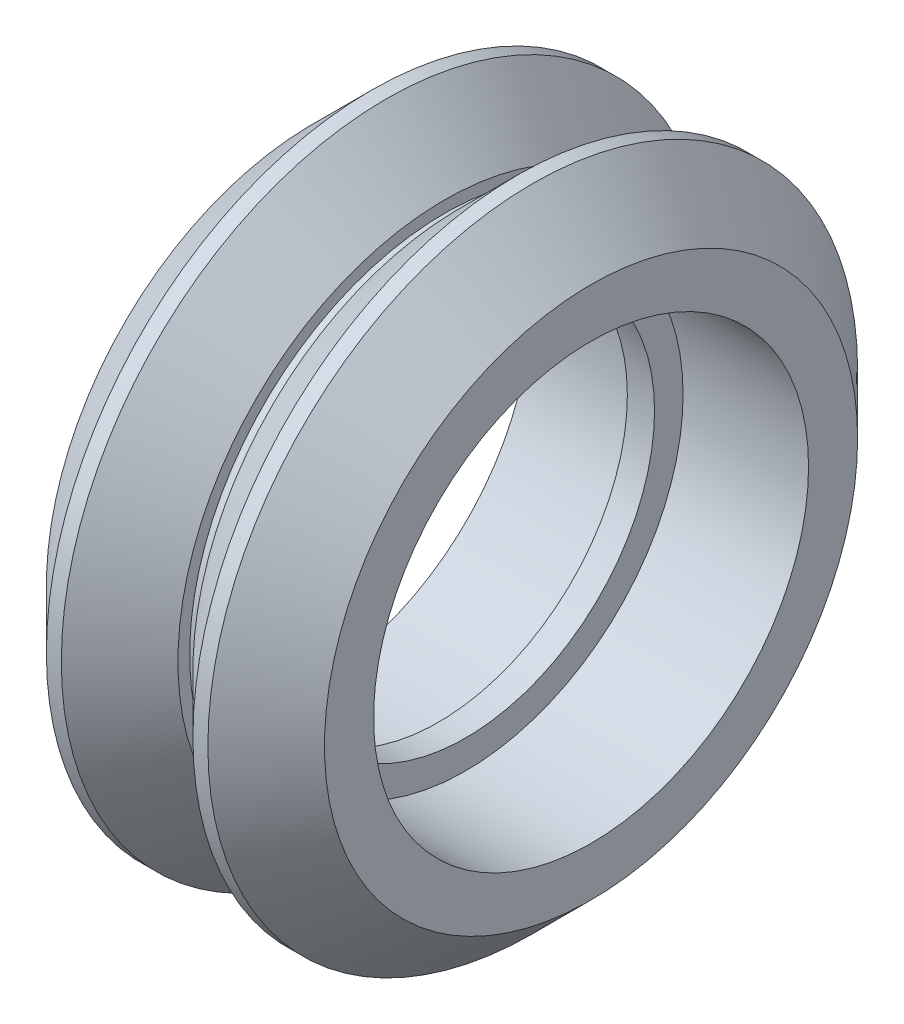
SolidWorks part; units mm, degrees
material "Delrin 2700 NC010, Low Viscosity Acetal Copolymer (SS)"
ref_plane "Front Plane" through (0, 0, 0) normal (0, 0, 1) x (1, 0, 0)
ref_plane "Top Plane" through (0, 0, 0) normal (0, 1, 0) x (1, 0, 0)
ref_plane "Right Plane" through (0, 0, 0) normal (1, 0, 0) x (0, 0, -1)
sketch "Sketch1" plane through (0, 0, 0) normal (0, 0, 1) x (1, 0, 0)
  line L0 (0.5, 6.95) -> (-0.5, 6.95)
  line L1 (-0.5, 6.95) -> (-0.5, 8)
  line L2 (-0.5, 8) -> (-5.115, 8)
  line L3 (-5.115, 8) -> (-5.115, 9.805)
  line L4 (-5.115, 9.805) -> (-2.97, 11.95)
  line L5 (-2.97, 11.95) -> (-2.42, 11.95)
  line L6 (0, 12) -> (0, 6.95) construction
  line L7 (5.115, 9.805) -> (2.97, 11.95)
  line L8 (5.115, 8) -> (5.115, 9.805)
  line L9 (0.5, 8) -> (5.115, 8)
  line L10 (0.5, 6.95) -> (0.5, 8)
  line L11 (0, 0) -> (-12.6359, 0) construction
  line L12 (-2.42, 11.95) -> (-0.275, 9.805)
  line L13 (-0.275, 9.805) -> (-0.275, 9.375)
  line L14 (-0.275, 9.375) -> (0.275, 9.375)
  line L15 (0.275, 9.805) -> (0.275, 9.375)
  line L16 (2.97, 11.95) -> (2.42, 11.95)
  line L17 (2.42, 11.95) -> (0.275, 9.805)
  point P20 (0, 9.375)
  dimension "D1" = 0.55
  dimension "D2" = 16
  dimension "D3" = 23.9
  dimension "D4" = 1
  dimension "D5" = 45
  dimension "D6" = 10.23
  dimension "D7" = 18.75
  dimension "D8" = 13.9
  dimension "D9" = 0.55
revolve "Revolve1" add sketch "Sketch1" angle 360 about L11
